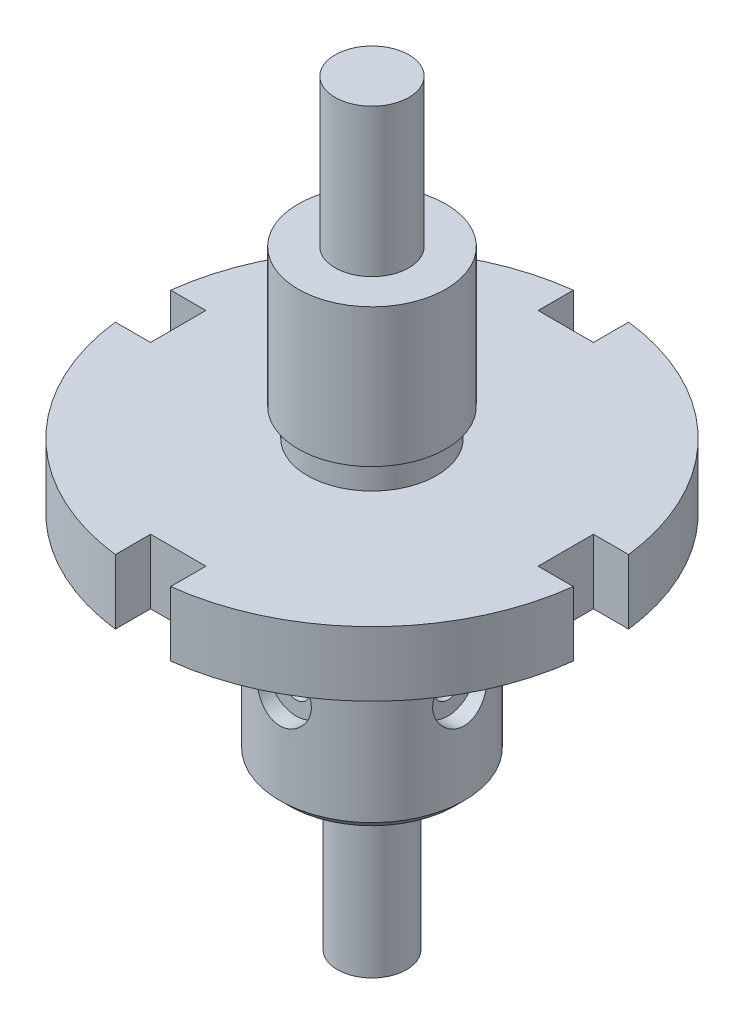
SolidWorks part; units mm, degrees
material "AISI 304"
ref_plane "Front Plane" through (0, 0, 0) normal (0, 0, 1) x (1, 0, 0)
ref_plane "Top Plane" through (0, 0, 0) normal (0, 1, 0) x (1, 0, 0)
ref_plane "Right Plane" through (0, 0, 0) normal (1, 0, 0) x (0, 0, -1)
sketch "Sketch1" plane through (0, 0, 0) normal (0, 0, 1) x (1, 0, 0)
  line L0 (0, 0) -> (0, 168.5699) construction
  line L1 (7.5, 0) -> (7.5, 30)
  line L2 (7.5, 30) -> (6, 30)
  line L3 (6, 30) -> (6, 36)
  line L4 (6, 36) -> (20, 36)
  line L5 (20, 36) -> (20, 76)
  line L6 (20, 76) -> (18, 76)
  line L7 (18, 76) -> (18, 82)
  line L8 (18, 82) -> (50, 82)
  line L9 (50, 82) -> (50, 96)
  line L10 (50, 96) -> (14, 96)
  line L11 (14, 96) -> (14, 102)
  line L12 (14, 102) -> (16, 102)
  line L13 (16, 102) -> (16, 132)
  line L14 (16, 132) -> (8, 132)
  line L15 (8, 132) -> (8, 164)
  line L16 (8, 164) -> (0, 164)
  line L17 (0, 164) -> (0, 0)
  line L18 (0, 0) -> (7.5, 0)
  dimension "D1" = 15
  dimension "D2" = 30
  dimension "D3" = 12
  dimension "D4" = 6
  dimension "D5" = 40
  dimension "D6" = 40
  dimension "D7" = 36
  dimension "D8" = 6
  dimension "D9" = 100
  dimension "D10" = 14
  dimension "D11" = 28
  dimension "D12" = 6
  dimension "D13" = 32
  dimension "D14" = 30
  dimension "D15" = 32
  dimension "D16" = 16
revolve "Revolve1" add sketch "Sketch1" angle 360 about L0
sketch "Sketch2" plane through (0, 96, 0) normal (0, 1, 0) x (1, 0, 0)
  line L0 (0, 0) -> (64.6744, 0) construction
  line L2 (42, 6) -> (49.6387, 6)
  line L3 (42, 6) -> (42, -6)
  line L4 (42, -6) -> (49.6387, -6)
  circle A0 centre (0, 0) radius 50 construction
  arc A1 (49.6387, -6) -> (49.6387, 6) centre (0, 0) ccw
  dimension "D1" = 42
  dimension "D2" = 12
extrude "Cut-Extrude1" cut sketch "Sketch2" against normal up to next (14 mm away)
pattern_circular "CirPattern1" count 4 over 360 about axis through (0, 0, 0) along (0, 1, 0) of "Cut-Extrude1"
ref_plane "Plane1" through (0, 0, 20) normal (0, 0, 1) x (1, 0, 0)
hole_wizard "CBORE for #12 Binding Head Machine Screw3" positions "Sketch5" profile "Sketch6" counterbore size "#12" standard "ANSI Inch"
sketch "Sketch5" plane through (0, 0, 20) normal (0, 0, 1) x (1, 0, 0)
  point P0 (0, 58)
  dimension "D1" = 58
sketch "Sketch6" plane through (0, 58, 20) normal (1, 0, 0) x (0, -1, 0)
  line L0 (0, 0) -> (0, 9.7399)
  line L1 (0, 9.7399) -> (2.8956, 8)
  line L2 (2.8956, 8) -> (2.8956, 3.5814)
  line L3 (2.8956, 3.5814) -> (5.9538, 3.5814)
  line L4 (5.9538, 3.5814) -> (5.9538, 0)
  line L5 (5.9538, 0) -> (0, 0)
  line L10 (0, 9.7399) -> (-2.8956, 8) construction
  line L11 (0, -6.35) -> (0, 107.95) construction
  dimension "Hole Dia." = 5.7912
  dimension "Hole Depth" = 8
  dimension "C'Bore Dia." = 11.9075
  dimension "C'Bore Depth" = 3.5814
  dimension "Drill Angle" = 118
pattern_circular "CirPattern2" count 4 over 360 about axis through (0, 0, 0) along (0, 1, 0) of "CBORE for #12 Binding Head Machine Screw3"
chamfer "Chamfer3" distance 2 angle 45 1 edges at (0, 36, -20)
